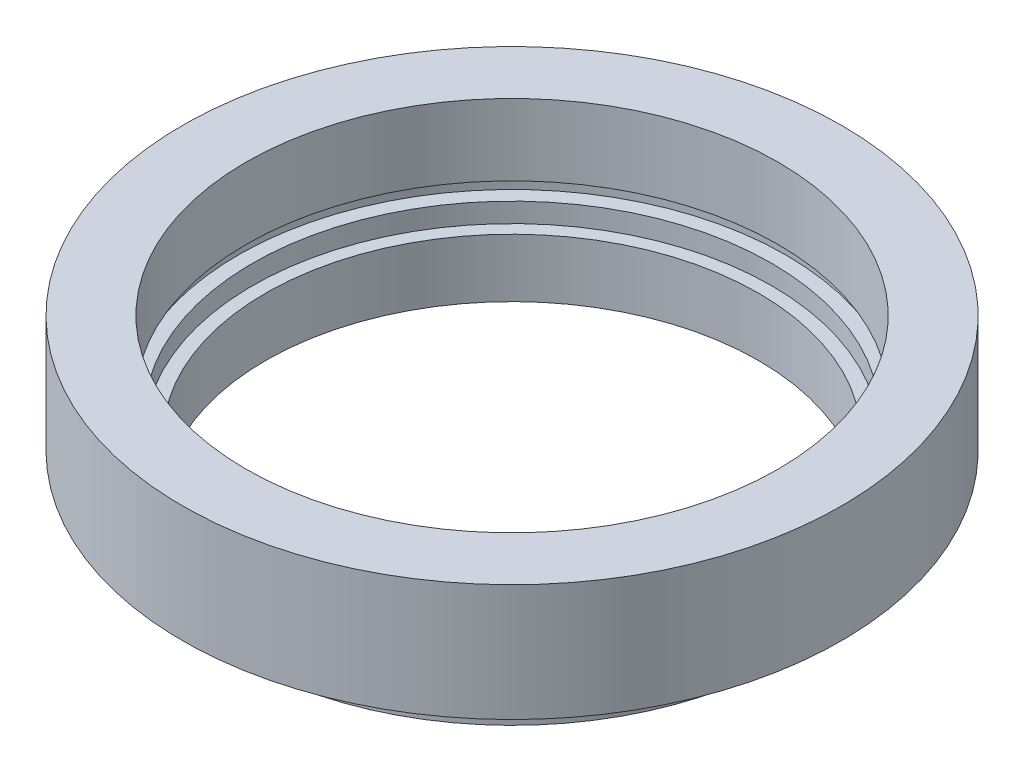
SolidWorks part; units mm, degrees
ref_plane "前视基准面" through (0, 0, 0) normal (0, 0, 1) x (1, 0, 0)
ref_plane "上视基准面" through (0, 0, 0) normal (0, 1, 0) x (1, 0, 0)
ref_plane "右视基准面" through (0, 0, 0) normal (1, 0, 0) x (0, 0, -1)
sketch "草图1" plane through (0, 0, 0) normal (0, 0, 1) x (1, 0, 0)
  line L0 (0, 0) -> (0, 21.8535) construction
  line L1 (19, 0) -> (21, 0)
  line L2 (21, 0) -> (21, 2.5)
  line L3 (21, 2.5) -> (20.5, 2.5)
  line L4 (20.5, 2.5) -> (20.5, 3.5)
  line L5 (20.5, 3.5) -> (25.4, 3.5)
  line L6 (25.4, 3.5) -> (25.4, 12.5)
  line L7 (25.4, 12.5) -> (20.5, 12.5)
  line L8 (20.5, 12.5) -> (20.5, 7)
  line L9 (20.5, 7) -> (21.1, 7)
  line L10 (21.1, 7) -> (21.1, 6)
  line L11 (21.1, 6) -> (20, 6)
  line L12 (20, 6) -> (20, 4.5)
  line L13 (20, 4.5) -> (19, 4.5)
  line L14 (19, 0) -> (19, 4.5)
  dimension "D1" = 12.5
  dimension "D2" = 25.4
  dimension "D3" = 20.5
  dimension "D4" = 20
  dimension "D5" = 1
  dimension "D6" = 1.5
  dimension "D7" = 19
  dimension "D8" = 21
  dimension "D9" = 1
  dimension "D10" = 3.5
  dimension "D11" = 4.5
  dimension "D12" = 21.1
  dimension "D13" = 20.5
revolve "旋转1" add sketch "草图1" angle 360 about L0
cosmetic thread "装饰螺纹线11" parameters "D2"=41
cosmetic thread "装饰螺纹线12" parameters "D2"=42
